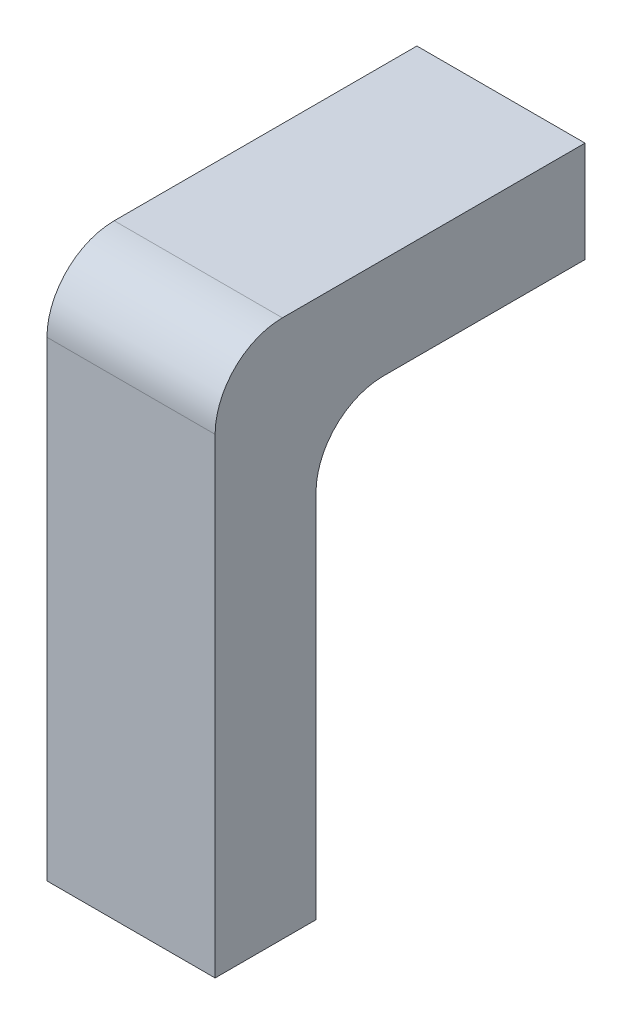
SolidWorks part; units mm, degrees
ref_plane "Спереди" through (0, 0, 0) normal (0, 0, 1) x (1, 0, 0)
ref_plane "Сверху" through (0, 0, 0) normal (0, 1, 0) x (1, 0, 0)
ref_plane "Справа" through (0, 0, 0) normal (1, 0, 0) x (0, 0, -1)
sketch "Эскиз1" plane through (0, 0, 0) normal (0, 1, 0) x (1, 0, 0)
  line L3 (-1.25, 0.75) -> (1.25, 0.75)
  line L4 (-1.25, 0.75) -> (-1.25, -0.75)
  line L5 (-1.25, -0.75) -> (1.25, -0.75)
  line L6 (1.25, 0.75) -> (1.25, -0.75)
  line L7 (-1.25, 0.75) -> (1.25, -0.75) construction
  line L8 (-1.25, -0.75) -> (1.25, 0.75) construction
  point P4 (0, 0)
  dimension "D4" = 2.5
  dimension "D6" = 1.5
extrude "Бобышка-Вытянуть1" add sketch "Эскиз1" along normal blind 8
sketch "Эскиз3" plane through (0, 8, 0) normal (0, 1, 0) x (1, 0, 0)
  line L2 (-1.25, -0.75) -> (1.25, -0.75)
  line L3 (-1.25, -0.75) -> (1.25, -0.75)
  line L8 (1.25, -0.75) -> (1.25, 0.75)
  line L9 (1.25, -0.75) -> (1.25, 0.75)
  line L10 (1.25, 0.75) -> (-1.25, 0.75)
  line L11 (1.25, 0.75) -> (-1.25, 0.75)
  line L12 (-1.25, 0.75) -> (-1.25, -0.75)
  line L13 (-1.25, 0.75) -> (-1.25, -0.75)
  dimension "D1" = 0
sketch "Эскиз5" plane through (0, 0, 0) normal (0, -1, 0) x (1, 0, 0)
  line L0 (1.25, 0) -> (-1.25, 0) construction
  line L1 (1.25, 0.75) -> (1.25, -0.75) construction
  line L2 (-1.25, -0.75) -> (-1.25, 0.75) construction
  circle A0 centre (0.535, 0) radius 0.435
  circle A1 centre (-0.535, 0) radius 0.435
  dimension "D1" = 0.87
  dimension "D2" = 0.87
  dimension "D3" = 0.535
  dimension "D4" = 1.07
extrude "Вырез-Вытянуть1" cut sketch "Эскиз5" against normal blind 3
sketch "Эскиз6" plane through (0, 0, -0.75) normal (0, 0, -1) x (-1, 0, 0)
  line L0 (-1.25, 8) -> (1.25, 8)
  line L1 (1.25, 8) -> (1.25, 6.5)
  line L2 (1.25, 8) -> (1.25, 0) construction
  line L3 (1.25, 6.5) -> (-1.25, 6.5)
  line L4 (-1.25, 8) -> (-1.25, 0) construction
  line L5 (-1.25, 6.5) -> (-1.25, 8)
  dimension "D1" = 1.5
  dimension "D2" = 2.5
extrude "Бобышка-Вытянуть2" add sketch "Эскиз6" along normal blind 4
fillet "Скругление1" radius 1 2 edges at (0, 8, 0.75) (0, 6.5, -0.75)
sketch "Эскиз7" plane through (0, 0, -4.75) normal (0, 0, -1) x (-1, 0, 0)
  line L0 (-1.25, 7.25) -> (1.25, 7.25) construction
  line L1 (-1.25, 8) -> (-1.25, 6.5) construction
  line L2 (1.25, 6.5) -> (1.25, 8) construction
  circle A0 centre (-0.535, 7.25) radius 0.435
  circle A1 centre (0.535, 7.25) radius 0.435
  point P10 (0, 7.25)
  point P11 (0, 0)
  point P12 (0, 0)
  dimension "D1" = 0.87
  dimension "D2" = 0.87
  dimension "D3" = 0.535
  dimension "D4" = 1.07
extrude "Вырез-Вытянуть2" cut sketch "Эскиз7" against normal blind 2
